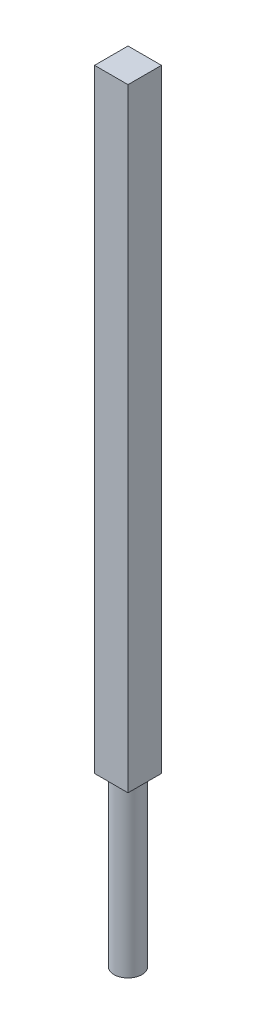
SolidWorks part; units mm, degrees
ref_plane "Front" through (0, 0, 0) normal (0, 0, 1) x (1, 0, 0)
ref_plane "Top" through (0, 0, 0) normal (0, 1, 0) x (1, 0, 0)
ref_plane "Right" through (0, 0, 0) normal (1, 0, 0) x (0, 0, -1)
sketch "Sketch1" plane through (0, 0, 0) normal (0, 1, 0) x (1, 0, 0)
  circle A0 centre (0, 0) radius 12.5
  dimension "D1" = 25
extrude "Boss-Extrude1" add sketch "Sketch1" along normal blind 150
sketch "Sketch2" plane through (0, 150, 0) normal (0, 1, 0) x (1, 0, 0)
  line L1 (-15, -15) -> (15, -15)
  line L2 (-15, -15) -> (-15, 15)
  line L3 (-15, 15) -> (15, 15)
  line L4 (15, -15) -> (15, 15)
  line L5 (-15, -15) -> (15, 15) construction
  line L6 (-15, 15) -> (15, -15) construction
  circle A1 centre (0, 0) radius 12.5 construction
  point P0 (0, 0)
  dimension "D1" = 30
  dimension "D2" = 30
  dimension "D3" = 12.5
extrude "Boss-Extrude2" add sketch "Sketch2" along normal blind 550
